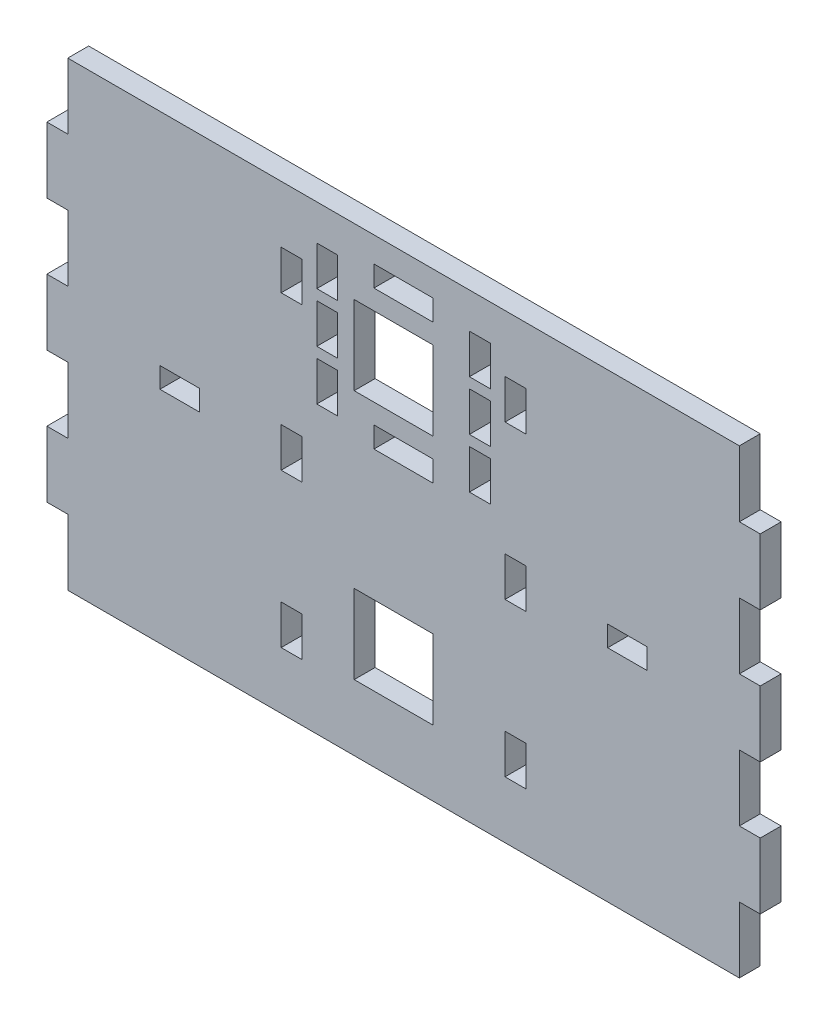
SolidWorks part; units mm, degrees
ref_plane "Front Plane" through (0, 0, 0) normal (0, 0, 1) x (1, 0, 0)
ref_plane "Top Plane" through (0, 0, 0) normal (0, 1, 0) x (1, 0, 0)
ref_plane "Right Plane" through (0, 0, 0) normal (1, 0, 0) x (0, 0, -1)
sketch "Sketch1" plane through (0, 0, 0) normal (0, 0, 1) x (1, 0, 0)
  line L0 (54.175, 5) -> (54.175, -5)
  line L1 (54.175, -25) -> (51, -25)
  line L2 (54.175, -15) -> (54.175, -25)
  line L3 (-51, 35) -> (-51, 25)
  line L4 (-51, 35) -> (51, 35)
  line L5 (0, 16.6227) -> (0, 8.5774) construction
  line L6 (23.0942, 0) -> (-1.5596, 0) construction
  line L7 (51, 25) -> (51, 35)
  line L8 (54.175, 5) -> (51, 5)
  line L9 (51, -15) -> (54.175, -15)
  line L10 (51, -5) -> (51, -15)
  line L11 (51, -25) -> (51, -35)
  line L12 (-51, -35) -> (51, -35)
  line L13 (-51, -25) -> (-51, -35)
  line L14 (54.175, -5) -> (51, -5)
  line L15 (0, 35) -> (0, -35) construction
  line L16 (4.5, 31.175) -> (-4.5, 31.175)
  line L17 (4.5, 31.175) -> (4.5, 28)
  line L18 (4.5, 28) -> (0, 28)
  line L19 (0, 28) -> (-4.5, 28)
  line L20 (-4.5, 28) -> (-4.5, 31.175)
  line L21 (-4.5, 10) -> (-4.5, 6.825)
  line L22 (0, 25) -> (4.5, 25)
  line L23 (4.5, 25) -> (4.5, 13)
  line L24 (-51, 35) -> (0, 35)
  line L25 (54.175, 0) -> (37, 0) construction
  line L26 (37, 1.5625) -> (31, 1.5625)
  line L27 (31, 1.5625) -> (31, -1.5625)
  line L28 (37, 1.5625) -> (37, -1.5625)
  line L29 (37, 0) -> (54.175, 0)
  line L30 (37, -1.5625) -> (31, -1.5625)
  line L31 (-37, -1.5625) -> (-31, -1.5625)
  line L32 (-37, 1.5625) -> (-37, -1.5625)
  line L33 (-31, 1.5625) -> (-31, -1.5625)
  line L34 (31, 0) -> (9.8, 0) construction
  line L35 (34, 1.5625) -> (34, 7.6646) construction
  line L36 (-51, 35) -> (0, 35)
  line L37 (18.5875, -3) -> (18.5875, 3)
  line L38 (18.5875, 3) -> (15.4125, 3)
  line L39 (15.4125, 3) -> (15.4125, -3)
  line L40 (17, 3) -> (17, 12.6102) construction
  line L41 (18.5875, -3) -> (15.4125, -3)
  line L42 (-18.5875, -3) -> (-15.4125, -3)
  line L43 (-15.4125, 3) -> (-15.4125, -3)
  line L44 (0, -35) -> (51, -35)
  line L45 (-17, 35) -> (-17, -35) construction
  line L46 (0, -35) -> (-51, -35)
  line L47 (0, 35) -> (51, 35)
  line L48 (17, 35) -> (17, -35) construction
  line L49 (-54.175, 25) -> (-51, 25)
  line L50 (-54.175, 15) -> (-54.175, 25)
  line L51 (-51, 15) -> (-54.175, 15)
  line L52 (-51, 5) -> (-51, 15)
  line L53 (51, 5) -> (51, 15)
  line L54 (51, 15) -> (54.175, 15)
  line L55 (54.175, 15) -> (54.175, 25)
  line L56 (54.175, 25) -> (51, 25)
  line L57 (-54.175, -5) -> (-51, -5)
  line L58 (-51, -5) -> (-51, -15)
  line L59 (-51, -15) -> (-54.175, -15)
  line L60 (-54.175, 5) -> (-51, 5)
  line L61 (-54.175, -15) -> (-54.175, -25)
  line L62 (-54.175, -25) -> (-51, -25)
  line L63 (-54.175, 5) -> (-54.175, -5)
  line L64 (55, 0) -> (-55, 0) construction
  line L65 (0, -55) -> (0, 55) construction
  line L66 (-37, 1.5625) -> (-31, 1.5625)
  line L67 (4.5, 13) -> (-7.5, 13)
  line L68 (0, 10) -> (-4.5, 10)
  line L69 (-7.5, 13) -> (-7.5, 25)
  line L70 (-17, 35) -> (17, 35)
  line L71 (17, 35) -> (51, 35)
  line L72 (-51, 35) -> (-17, 35)
  line L73 (17, 35) -> (51, 35)
  line L74 (-7.5, 25) -> (0, 25)
  line L75 (-18.5875, 3) -> (-15.4125, 3)
  line L76 (34, 35) -> (34, -35) construction
  line L77 (-18.5875, -3) -> (-18.5875, 3)
  line L78 (-17, 35) -> (-17, 11.6667) construction
  line L79 (-17, 11.6667) -> (-17, -11.6667) construction
  line L80 (-17, -11.6667) -> (-17, -35) construction
  line L81 (-17, 20.3333) -> (-17, 23.3333) construction
  line L82 (-18.5875, 23.3333) -> (-18.5875, 26.3333)
  line L83 (-18.5875, 26.3333) -> (-15.4125, 26.3333)
  line L84 (-17, 23.3333) -> (-18.5875, 23.3333) construction
  line L85 (-15.4125, 26.3333) -> (-15.4125, 20.3333)
  line L86 (-15.4125, 20.3333) -> (-18.5875, 20.3333)
  line L87 (-18.5875, 20.3333) -> (-18.5875, 23.3333)
  line L88 (17, 23.3333) -> (18.5875, 23.3333) construction
  line L89 (17, 20.3333) -> (17, 23.3333) construction
  line L90 (18.5875, 20.3333) -> (18.5875, 23.3333)
  line L91 (15.4125, 20.3333) -> (18.5875, 20.3333)
  line L92 (15.4125, 26.3333) -> (15.4125, 20.3333)
  line L93 (18.5875, 26.3333) -> (15.4125, 26.3333)
  line L94 (18.5875, 23.3333) -> (18.5875, 26.3333)
  line L95 (17, -20.3333) -> (17, -23.3333) construction
  line L96 (17, -23.3333) -> (18.5875, -23.3333) construction
  line L97 (18.5875, -23.3333) -> (18.5875, -26.3333)
  line L98 (18.5875, -26.3333) -> (15.4125, -26.3333)
  line L99 (15.4125, -26.3333) -> (15.4125, -20.3333)
  line L100 (15.4125, -20.3333) -> (18.5875, -20.3333)
  line L101 (18.5875, -20.3333) -> (18.5875, -23.3333)
  line L102 (-17, -23.3333) -> (-18.5875, -23.3333) construction
  line L103 (-17, -20.3333) -> (-17, -23.3333) construction
  line L104 (-18.5875, -20.3333) -> (-18.5875, -23.3333)
  line L105 (-15.4125, -20.3333) -> (-18.5875, -20.3333)
  line L106 (-15.4125, -26.3333) -> (-15.4125, -20.3333)
  line L107 (-18.5875, -26.3333) -> (-15.4125, -26.3333)
  line L108 (-18.5875, -23.3333) -> (-18.5875, -26.3333)
  line L109 (-2.5481, 19) -> (-5.0089, 19) construction
  line L110 (-10, 19) -> (-10, 22)
  line L111 (-10, 22) -> (-13.175, 22)
  line L112 (-13.175, 22) -> (-13.175, 16)
  line L113 (-13.175, 16) -> (-10, 16)
  line L114 (-10, 16) -> (-10, 19)
  line L115 (-10, 23.5875) -> (-10, 29.5875)
  line L116 (-10, 29.5875) -> (-13.175, 29.5875)
  line L117 (-13.175, 29.5875) -> (-13.175, 23.5875)
  line L118 (-13.175, 23.5875) -> (-10, 23.5875)
  line L119 (-10, 14.4125) -> (-13.175, 14.4125)
  line L120 (-13.175, 14.4125) -> (-13.175, 8.4125)
  line L121 (-13.175, 8.4125) -> (-10, 8.4125)
  line L122 (-10, 8.4125) -> (-10, 14.4125)
  line L123 (-11.5875, 22) -> (-11.5875, 23.5875)
  line L124 (-11.5875, 16) -> (-11.5875, 14.4125)
  line L125 (4.5, 10) -> (0, 10)
  line L126 (4.5, 6.825) -> (4.5, 10)
  line L127 (4.5, 6.825) -> (-4.5, 6.825)
  line L128 (11.5875, 16) -> (11.5875, 14.4125)
  line L129 (11.5875, 22) -> (11.5875, 23.5875)
  line L130 (10, 8.4125) -> (10, 14.4125)
  line L131 (13.175, 8.4125) -> (10, 8.4125)
  line L132 (13.175, 14.4125) -> (13.175, 8.4125)
  line L133 (10, 14.4125) -> (13.175, 14.4125)
  line L134 (13.175, 23.5875) -> (10, 23.5875)
  line L135 (13.175, 29.5875) -> (13.175, 23.5875)
  line L136 (10, 29.5875) -> (13.175, 29.5875)
  line L137 (10, 23.5875) -> (10, 29.5875)
  line L138 (10, 16) -> (10, 19)
  line L139 (13.175, 16) -> (10, 16)
  line L140 (13.175, 22) -> (13.175, 16)
  line L141 (10, 22) -> (13.175, 22)
  line L142 (10, 19) -> (10, 22)
  line L143 (-7.5, 19) -> (-1.5127, 19) construction
  line L144 (-7.5, 13) -> (0, 13)
  line L145 (4.5, 25) -> (-7.5, 25)
  line L146 (0, 13) -> (4.5, 13)
  line L147 (0, 25) -> (4.5, 25)
  line L148 (4.5, 13) -> (-7.5, 13)
  line L149 (-7.5, 25) -> (0, 25)
  line L150 (-7.5, 13) -> (0, 13)
  line L151 (4.5, 25) -> (-7.5, 25)
  line L152 (0, 13) -> (4.5, 13)
  line L153 (-51, 35) -> (-17, 35)
  line L154 (0, -13) -> (4.5, -13)
  line L155 (4.5, -25) -> (-7.5, -25)
  line L156 (-7.5, -13) -> (0, -13)
  line L157 (-7.5, -25) -> (0, -25)
  line L158 (4.5, -13) -> (-7.5, -13)
  line L159 (0, -25) -> (4.5, -25)
  line L160 (0, -13) -> (4.5, -13)
  line L161 (4.5, -25) -> (-7.5, -25)
  line L162 (-7.5, -13) -> (0, -13)
  line L163 (-7.5, -25) -> (0, -25)
  line L164 (-7.5, -13) -> (-7.5, -25)
  line L165 (4.5, -13) -> (-7.5, -13)
  line L166 (4.5, -25) -> (4.5, -13)
  line L167 (0, -25) -> (4.5, -25)
  line L168 (-34, 35) -> (-34, -35) construction
  point P0 (-2.7216, -35)
  point P17 (81.35, 0)
  point P22 (-81.35, 0)
  point P60 (15.4125, 0)
  point P89 (18.5875, 0)
  point P93 (-18.5875, 0)
  point P94 (-15.4125, 0)
  dimension "D2" = 6
  dimension "D3" = 3.175
  dimension "D4" = 102
  dimension "D5" = 12
  dimension "D6" = 4.5
  dimension "D7" = 6
  dimension "D8" = 1.5625
  dimension "D9" = 3.175
  dimension "D10" = 3
  dimension "D11" = 9
  dimension "D12" = 12
  dimension "D13" = 1.5875
  dimension "D14" = 3.175
  dimension "D15" = 70
  dimension "D16" = 20
  dimension "D17" = 3.175
  dimension "D18" = 18
extrude "Boss-Extrude1" add sketch "Sketch1" along normal mid plane 3.175
